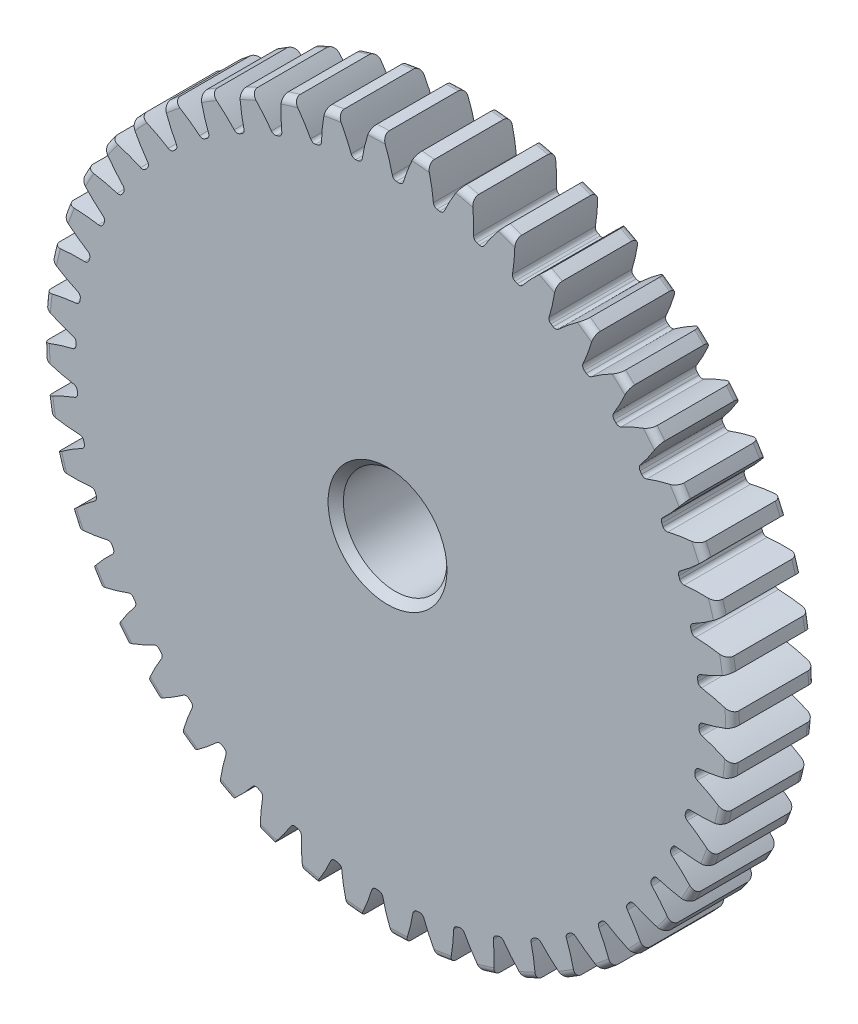
SolidWorks part; units mm, degrees
ref_plane "Front" through (0, 0, 0) normal (0, 0, 1) x (1, 0, 0)
ref_plane "Top" through (0, 0, 0) normal (0, 1, 0) x (1, 0, 0)
ref_plane "Right" through (0, 0, 0) normal (1, 0, 0) x (0, 0, -1)
sketch "Sketch1" plane through (0, 0, 0) normal (0, 0, 1) x (1, 0, 0)
  line L0 (-609.6, 0) -> (609.6, 0) construction
  circle A0 centre (0, 0) radius 26.416
  circle A1 centre (0, 0) radius 25.4 construction
  circle A3 centre (0, 0) radius 24.1755 construction
  dimension "D1" = 1.2245
  dimension "D2" = 2.2405
  dimension "D3" = 1.016
extrude "Boss-Extrude1" add sketch "Sketch1" against normal blind 6.35
sketch "Sketch2" plane through (0, 0, 0) normal (1, 0, 0) x (0, 0, -1)
  line L0 (6.35, 0) -> (14.224, 0)
  line L1 (6.35, 0) -> (6.35, 11.7078)
  line L2 (6.35, 11.7078) -> (14.224, 11.7078)
  line L3 (14.224, 11.7078) -> (14.224, 0)
  point P5 (14.224, -11.7078)
  point P6 (0, -26.416)
  point P7 (6.35, -26.416)
  point P9 (0, 26.416)
revolve "Revolve1" add sketch "Sketch2" angle 360 mid plane about L0
fillet "Fillet2" radius 0.5283 3 edges at (26.416, 0, -6.35) (26.416, 0, 0) (11.7078, 0, -6.35)
sketch "Sketch3" plane through (0, 0, 0) normal (0, 0, 1) x (1, 0, 0)
  line L0 (0, 0) -> (0, 26.416) construction
  line L1 (-8.1634, 22.4288) -> (0, 25.4)
  line L2 (-9.5921, 25.4) -> (9.5921, 25.4) construction
  line L3 (-9.0136, 22.1193) -> (9.0136, 28.6807) construction
  line L4 (-8.1634, 22.4288) -> (0, 0) construction
  line L5 (-19.9021, 13.1757) -> (0, 0) construction
  line L6 (-19.9021, 13.1757) -> (-6.7143, 33.096) construction
  line L7 (-5.6706, 23.1848) -> (0, 0) construction
  line L8 (-5.6706, 23.1848) -> (0.2364, 24.6296) construction
  arc A0 (-8.1634, 22.4288) -> (-19.9021, 13.1757) centre (0, 0) ccw
  circle A1 centre (0, 0) radius 25.4 construction
  circle A2 centre (0, 0) radius 23.8682 construction
  arc A3 (-8.1634, 22.4288) -> (-5.6706, 23.1848) centre (0, 0) cw
  circle A4 centre (0, 0) radius 26.416 construction
  point P6 (0, 25.4)
  dimension "D1" = 8.6873
  dimension "D3" = 23.8901
  dimension "D5" = 6.0811
  dimension "D2" = 15.2028
  dimension "D4" = 2.6062
sketch "Sketch4" plane through (0, 0, 0) normal (0, 0, 1) x (1, 0, 0)
  line L0 (0, 0) -> (0.8306, 25.3728) construction
  line L2 (0, 25.4) -> (1.6612, 25.3456) construction
  line L4 (0.4216, 23.8645) -> (0, 0) construction
  line L6 (-19.9021, 13.1757) -> (-6.7143, 33.096) construction
  line L7 (-19.9021, 13.1757) -> (-6.7143, 33.096) construction
  arc A0 (1.1401, 23.8409) -> (0.4216, 23.8645) centre (0, 0) ccw
  arc A1 (0, 25.4) -> (1.6612, 25.3456) centre (0, 0) cw construction
  circle A2 centre (0, 0) radius 25.4 construction
  circle A3 centre (0, 0) radius 23.8682 construction
  arc A5 (8.8645, 32.586) -> (-6.7143, 33.096) centre (0, 0) ccw
  spline S0 degree 2 poles (-6.7143, 33.096) (-0.803, 29.6485) (0.4216, 23.8645) knots 0 0 0 1 1 1
  spline S1 degree 2 poles (8.8645, 32.586) (2.7403, 29.5325) (1.1401, 23.8409) knots 0 0 0 1 1 1
  dimension "D1" = 1.6624
extrude "Cut-Extrude1" cut sketch "Sketch4" against normal through all
fillet "Fillet1" radius 0.3325 2 edges at (1.1401, 23.8409, -3.175) (0.4216, 23.8645, -3.175)
pattern_circular "CirPattern1" count 48 over 360 about axis through (0, 0, -6.35) along (0, 0, 1) of "Cut-Extrude1", "Fillet1"
sketch "Sketch5" plane through (0, 0, 0) normal (0, 0, 1) x (1, 0, 0)
  circle A0 centre (0, 0) radius 3.9688
  circle A1 centre (0, 0) radius 3.9688 construction
  dimension "Bore Min" = 7.9375
  dimension "Bore Max" = 7.9375
extrude "Cut-Extrude2" cut sketch "Sketch5" against normal through all
chamfer "Chamfer1" distance 0.5854 angle 45 3 edges at (11.7078, 0, -14.224) (3.9688, 0, 0) (3.9688, 0, -14.224)
sketch "Pitch Dia" plane through (0, 0, 0) normal (0, 0, 1) x (1, 0, 0)
  circle A0 centre (0, 0) radius 25.4 construction
  circle A1 centre (0, 0) radius 25.4 construction
sketch "Sketch6" plane through (0, 0, 0) normal (0, 0, 1) x (1, 0, 0)
  line L0 (-1.3337, 26.3823) -> (-0.3947, 26.4131)
  line L1 (-0.8642, 26.3977) -> (-0.7719, 23.5785) construction
  arc A0 (-2.2394, 23.7629) -> (-1.9424, 24.0403) centre (-2.2706, 24.0939) ccw construction
  arc A1 (-2.2394, 23.7629) -> (-2.4396, 23.7432) centre (0, 0) ccw construction
  arc A2 (0.366, 24.1159) -> (0.6804, 23.8585) centre (0.6899, 24.1908) ccw construction
  arc A3 (0.8815, 23.8519) -> (0.6804, 23.8585) centre (0, 0) ccw construction
  parabola Q2 (-1.5162, 25.8432) -> (-1.3337, 26.3823) focus (4.6524, 24.5229) apex (-1.1149, 26.9412) construction
  parabola Q3 (-1.9424, 24.0403) -> (-1.5162, 25.8432) focus (4.6524, 24.5229) apex (-1.1149, 26.9412) construction
  parabola Q4 (-1.9424, 24.0403) -> (-1.5162, 25.8432) focus (4.6524, 24.5229) apex (-1.1149, 26.9412) construction
  parabola Q5 (-1.9424, 24.0403) -> (-1.5162, 25.8432) focus (4.6524, 24.5229) apex (-1.1149, 26.9412) construction
  parabola Q6 (-1.9424, 24.0403) -> (-1.5162, 25.8432) focus (4.6524, 24.5229) apex (-1.1149, 26.9412) construction
  spline S0 degree 3 poles (-1.3337, 26.3823) (-1.3986, 26.204) (-1.4881, 25.9395) (-1.6086, 25.5407) (-1.6684, 25.3219) (-1.7024, 25.1889) knots 0 0 0 0 0.455486 0.670301 1 1 1 1
  spline S1 degree 3 poles (-1.7024, 25.1889) (-1.7636, 24.906) (-1.8284, 24.543) (-1.924, 24.1631) (-1.9413, 24.0397) (-1.9588, 23.9693) (-1.9959, 23.9009) (-2.0556, 23.8348) (-2.1669, 23.7641) (-2.2735, 23.7587) (-2.3395, 23.7533) knots 0 0 0 0 0.50758 0.647219 0.68628 0.726157 0.773713 0.821128 0.881401 1 1 1 1
  spline S2 degree 3 poles (-0.3947, 26.4131) (-0.3182, 26.2394) (-0.2116, 25.9813) (-0.0653, 25.5913) (0.0087, 25.3768) (0.0514, 25.2463) knots 0 0 0 0 0.455486 0.670301 1 1 1 1
  spline S3 degree 3 poles (0.0514, 25.2463) (0.1141, 25.0361) (0.1742, 24.7693) (0.2761, 24.4493) (0.321, 24.282) (0.3561, 24.146) (0.3832, 24.0582) (0.4097, 24.0095) (0.4401, 23.969) (0.4848, 23.9267) (0.5415, 23.8901) (0.6424, 23.8533) (0.7263, 23.8582) (0.7809, 23.8554) knots 0 0 0 0 0.384807 0.478666 0.588978 0.688379 0.725395 0.749588 0.785292 0.813657 0.857185 0.902571 1 1 1 1
equation "\"D1@Boss-Extrude1\" = \"Face Wd@Sketch2\""
equation "\"D2@Sketch3\" = \"D1@Sketch3\"*1.75"
equation "\"D3@Sketch3\" = \"D1@Sketch3\"+\"D2@Sketch3\""
equation "\"D4@Sketch3\" = \"D1@Sketch3\"*.3"
equation "\"D5@Sketch3\" = \"D1@Sketch3\"-\"D4@Sketch3\""
equation "\"D1@Sketch4\" = 1.5708/(\"Number of Teeth@Sketch1\"/\"Ptich Dia@Sketch1\")"
equation "\"D1@Chamfer1\" = \"B Hub Dia@Sketch2\"*.025"
equation "\"D1@CirPattern1\" = \"Number of Teeth@Sketch1\""
equation "\"D1@Fillet1\" = \"D1@Sketch4\"*.2"
equation "\"D1@Fillet2\" = \"OD@Sketch1\"*.01"
equation "\"D1@Sketch1\" = 1.157/(\"Number of Teeth@Sketch1\"/\"Ptich Dia@Sketch1\")"
